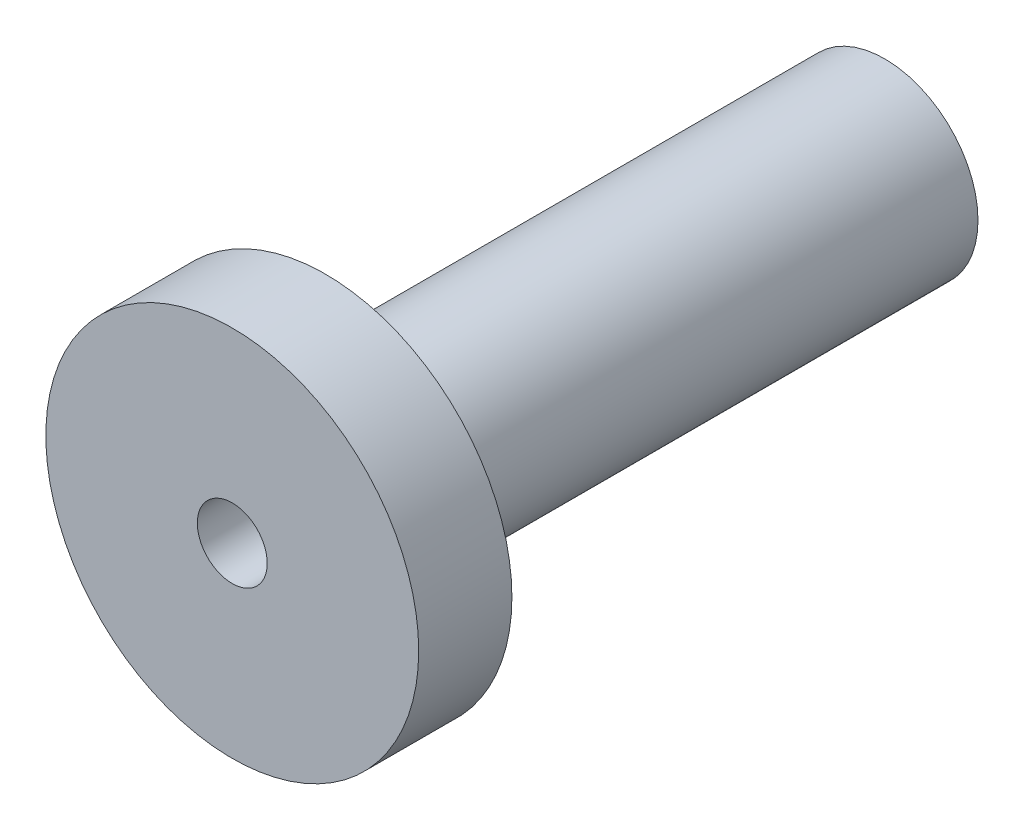
SolidWorks part; units mm, degrees
ref_plane "Front Plane" through (0, 0, 0) normal (0, 0, 1) x (1, 0, 0)
ref_plane "Top Plane" through (0, 0, 0) normal (0, 1, 0) x (1, 0, 0)
ref_plane "Right Plane" through (0, 0, 0) normal (1, 0, 0) x (0, 0, -1)
sketch "Sketch1" plane through (0, 0, 0) normal (1, 0, 0) x (0, 0, -1)
  line L0 (0, 0) -> (14, 0)
  line L1 (14, 0) -> (14, -2)
  line L2 (14, -2) -> (2, -2)
  line L3 (2, -2) -> (2, -4)
  line L4 (2, -4) -> (0, -4)
  line L5 (0, -4) -> (0, 0)
  dimension "D1" = 2
  dimension "D2" = 4
  dimension "D3" = 12
  dimension "D4" = 2
revolve "Revolve1" add sketch "Sketch1" angle 360 about L0
sketch "Sketch2" plane through (0, 0, -14) normal (0, 0, -1) x (-1, 0, 0)
  circle A0 centre (0, 0) radius 0.75
  dimension "D1" = 1.5
extrude "Cut-Extrude1" cut sketch "Sketch2" against normal through all
